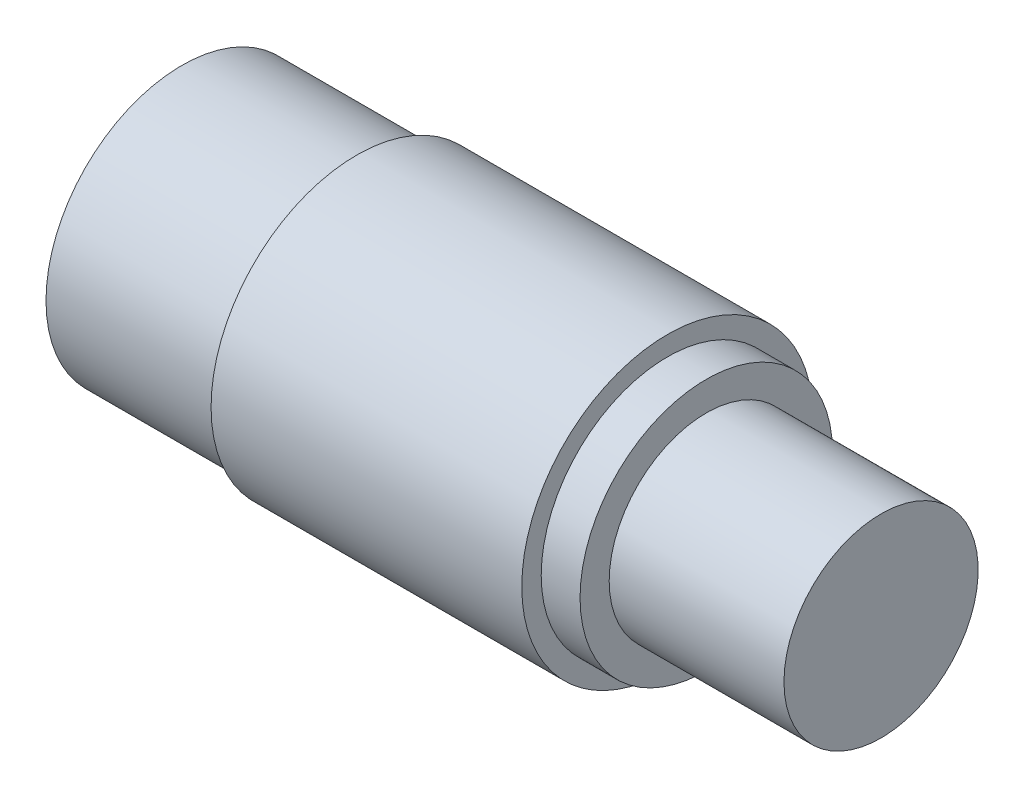
SolidWorks part; units mm, degrees
ref_plane "前基準面" through (0, 0, 0) normal (0, 0, 1) x (1, 0, 0)
ref_plane "上基準面" through (0, 0, 0) normal (0, 1, 0) x (1, 0, 0)
ref_plane "右基準面" through (0, 0, 0) normal (1, 0, 0) x (0, 0, -1)
sketch "草圖1" plane through (0, 0, 0) normal (0, 0, 1) x (1, 0, 0)
  line L0 (-48.335, 0) -> (49.9023, 0) construction
  line L1 (-18, 0) -> (-18, 7)
  line L2 (-18, 7) -> (-9, 7)
  line L3 (-9, 7) -> (-9, 7.5)
  line L4 (-9, 7.5) -> (7, 7.5)
  line L5 (7, 7.5) -> (7, 6.5)
  line L6 (7, 6.5) -> (9, 6.5)
  line L7 (9, 6.5) -> (9, 5)
  line L8 (9, 5) -> (18, 5)
  line L9 (18, 5) -> (18, 0)
  line L10 (18, 0) -> (-18, 0)
  point P5 (0, 0)
  dimension "D1" = 14
  dimension "D2" = 10
  dimension "D3" = 9
  dimension "D4" = 9
  dimension "D5" = 18
  dimension "D6" = 13
  dimension "D7" = 15
  dimension "D8" = 2
revolve "旋轉1" add sketch "草圖1" angle 360 about L0
